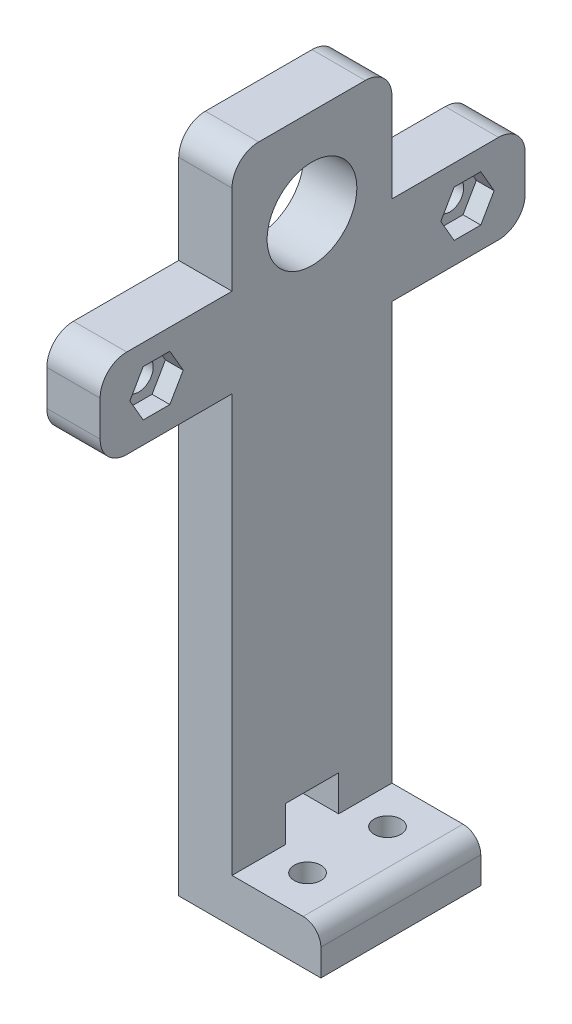
SolidWorks part; units mm, degrees
ref_plane "Front Plane" through (0, 0, 0) normal (0, 0, 1) x (1, 0, 0)
ref_plane "Top Plane" through (0, 0, 0) normal (0, 1, 0) x (1, 0, 0)
ref_plane "Right Plane" through (0, 0, 0) normal (1, 0, 0) x (0, 0, -1)
sketch "Sketch1" plane through (0, 0, 0) normal (0, 1, 0) x (1, 0, 0)
  circle A0 centre (0, 0) radius 17.45
  circle A1 centre (0, 0) radius 12.45
  dimension "D1" = 5
  dimension "D2" = 34.9
extrude "Boss-Extrude1" add sketch "Sketch1" along normal blind 8
sketch "Sketch2" plane through (0, 8, 0) normal (0, 1, 0) x (1, 0, 0)
  circle A0 centre (0, 0) radius 12.45
  circle A1 centre (0, 0) radius 20
  dimension "D1" = 40
extrude "Boss-Extrude2" add sketch "Sketch2" along normal blind 2
sketch "Sketch3" plane through (0, 10, 0) normal (0, 1, 0) x (1, 0, 0)
  circle A0 centre (0, 0) radius 12.45
  circle A1 centre (0, 0) radius 32.5
  dimension "D1" = 65
extrude "Boss-Extrude3" add sketch "Sketch3" along normal blind 4
fillet "Fillet1" radius 1 1 edges at (0, 14, 32.5)
sketch "Sketch10" plane through (0, 14, 0) normal (0, 1, 0) x (1, 0, 0)
  line L1 (30.1869, 9) -> (40.1869, 9)
  line L2 (30.1869, 9) -> (30.1869, -9)
  line L3 (30.1869, -9) -> (40.1869, -9)
  line L4 (40.1869, 9) -> (40.1869, -9)
  line L5 (-30.1869, 9) -> (-40.1869, 9)
  line L6 (-30.1869, 9) -> (-30.1869, -9)
  line L7 (-30.1869, -9) -> (-40.1869, -9)
  line L8 (-40.1869, 9) -> (-40.1869, -9)
  circle A0 centre (0, 0) radius 31.5 construction
  dimension "D1" = 10
  dimension "D2" = 18
extrude "Boss-Extrude6" add sketch "Sketch10" along normal offset from surface (4 mm away) 4 from surface at -4 up to face at (0, 10, 20) starting at face at (0, 10, 20)
sketch "Sketch4" plane through (0, 14, 0) normal (0, 1, 0) x (1, 0, 0)
  line L0 (34.1869, 0) -> (-34.1869, 0) construction
  line L2 (-34.1869, 9) -> (-34.1869, -9)
  line L8 (34.1869, 9) -> (34.1869, -9)
  line L10 (34.1869, 9) -> (40.1869, 9)
  line L11 (40.1869, 9) -> (40.1869, -9)
  line L12 (40.1869, -9) -> (34.1869, -9)
  line L13 (-34.1869, 9) -> (-40.1869, 9)
  line L14 (-40.1869, 9) -> (-40.1869, -9)
  line L15 (-40.1869, -9) -> (-34.1869, -9)
  point P8 (0, 0)
  dimension "D1" = 6
extrude "Boss-Extrude4" add sketch "Sketch4" along normal blind 75 and the other way blind 4
sketch "Sketch5" plane through (34.1869, 0, 0) normal (-1, 0, 0) x (0, 0, 1)
  line L0 (-9, 14) -> (9, 14) construction
  line L1 (-9, 89) -> (9, 89) construction
  circle A0 centre (0, 79) radius 5.05
  point P7 (0, 89)
  dimension "D1" = 10.1
  dimension "D2" = 65
extrude "Cut-Extrude1" cut sketch "Sketch5" against normal blind 113 and the other way blind 306
sketch "Sketch6" plane through (0, 0, -9) normal (0, 0, -1) x (-1, 0, 0)
  line L1 (34.1869, 75.95) -> (40.1869, 75.95)
  line L2 (34.1869, 75.95) -> (34.1869, 65.95)
  line L3 (34.1869, 65.95) -> (40.1869, 65.95)
  line L4 (40.1869, 75.95) -> (40.1869, 65.95)
  line L6 (40.1869, 89) -> (40.1869, 10) construction
  line L7 (34.1869, 14) -> (34.1869, 89) construction
  dimension "D1" = 10
  dimension "D2" = 8
extrude "Boss-Extrude5" add sketch "Sketch6" along normal blind 15 and the other way blind 32.85
sketch "Sketch7" plane through (-34.1869, 0, 0) normal (1, 0, 0) x (0, 0, -1)
  line L0 (-17.5, 71) -> (17.5, 71) construction
  circle A0 centre (-17.5, 71) radius 1.6292
  circle A1 centre (17.5, 71) radius 1.5803
  circle A3 centre (0, 79) radius 4.05 construction
  point P6 (0, 71)
  dimension "D2" = 8
  dimension "D1" = 35
  dimension "D3" = 17.5
extrude "Cut-Extrude2" cut sketch "Sketch7" against normal blind 10
sketch "Sketch9" plane through (-34.1869, 0, 0) normal (1, 0, 0) x (0, 0, -1)
  circle A0 centre (0, 79) radius 5.05
  dimension "D1" = 10.1
extrude "Cut-Extrude3" cut sketch "Sketch9" against normal blind 10 and the other way blind 10
sketch "Sketch11" plane through (34.1869, 0, 0) normal (-1, 0, 0) x (0, 0, 1)
  line L0 (-9, 14) -> (9, 14) construction
  line L1 (4.8913, 14) -> (-4.8913, 14)
  line L2 (4.8913, 14) -> (4.8913, 17.2345)
  line L3 (4.8913, 17.2345) -> (-4.8913, 17.2345)
  line L4 (-4.8913, 14) -> (-4.8913, 17.2345)
  line L5 (9, 10) -> (-9, 10) construction
  point P6 (0, 14)
  point P9 (0, 10)
extrude "Cut-Extrude4" cut sketch "Sketch11" against normal blind 61 and the other way blind 123
fillet "Fillet4" radius 3 6 edges at (-37.1869, 65.95, 23.85) (-37.1869, 75.95, 23.85) (-37.1869, 65.95, -24) (-37.1869, 75.95, -24) (-37.1869, 89, -9) (-37.1869, 89, 9)
fillet "Fillet5" radius 3 2 edges at (40.1869, 10, 0) (-40.1869, 10, 0)
sketch "Sketch12" plane through (40.1869, 0, 0) normal (1, 0, 0) x (0, 0, -1)
  line L0 (9, 10) -> (-9, 10) construction
  line L1 (41.8928, 10) -> (-66.8986, 10)
  line L2 (41.8928, 10) -> (41.8928, -14.0418)
  line L3 (41.8928, -14.0418) -> (-66.8986, -14.0418)
  line L4 (-66.8986, 10) -> (-66.8986, -14.0418)
extrude "Cut-Extrude5" cut sketch "Sketch12" against normal blind 110.678
sketch "Sketch15" plane through (0, 14, 0) normal (0, 1, 0) x (1, 0, 0)
  circle A0 centre (0, 0) radius 22
  dimension "D1" = 44
extrude "Cut-Extrude7" cut sketch "Sketch15" against normal blind 4
sketch "Sketch13" plane through (0, 14, 0) normal (0, 1, 0) x (1, 0, 0)
  line L0 (-15.1554, -8.75) -> (0, 17.5) construction
  line L1 (0, 17.5) -> (15.1554, -8.75) construction
  line L2 (15.1554, -8.75) -> (-15.1554, -8.75) construction
  circle A0 centre (0, 0) radius 11
  circle A1 centre (0, 0) radius 22
  circle A2 centre (0, 0) radius 17.5 construction
  circle A3 centre (0, 17.5) radius 2.75
  circle A4 centre (-15.1554, -8.75) radius 2.75
  circle A5 centre (15.1554, -8.75) radius 2.75
  dimension "D1" = 22
  dimension "D2" = 5.5
  dimension "D3" = 44
  dimension "D5" = 35
  dimension "D4" = 60
extrude "Boss-Extrude7" add sketch "Sketch13" against normal blind 4
fillet "Fillet6" radius 3 2 edges at (37.1869, 89, -9) (37.1869, 89, 9)
sketch "Sketch16" plane through (0, 10, 0) normal (0, -1, 0) x (1, 0, 0)
  line L0 (-31.229, 9) -> (-20.2938, 9)
  line L1 (31.229, 9) -> (20.2938, 9)
  arc A0 (-31.229, 9) -> (31.229, 9) centre (0, 0) cw
  arc A1 (-20.2938, 9) -> (20.2938, 9) centre (0, 0) cw
  dimension "D1" = 22.2
extrude "Cut-Extrude8" cut sketch "Sketch16" against normal blind 5
mirror "Mirror1" about plane through (0, 0, 0) normal (0, 0, 1) of "Cut-Extrude8"
fillet "Fillet7" radius 1 2 edges at (0, 14, 22.2) (0, 14, -22.2)
sketch "Sketch17" plane through (0, 10, 0) normal (0, -1, 0) x (1, 0, 0)
  line L0 (20.2938, -9) -> (40.1869, -9)
  line L1 (40.1869, -9) -> (40.1869, 9)
  line L2 (40.1869, 9) -> (20.2938, 9)
  arc A0 (20.2938, -9) -> (20.2938, 9) centre (0, 0) ccw
  arc A1 (-20.2938, -9) -> (20.2938, -9) centre (0, 0) ccw construction
extrude "Boss-Extrude8" add sketch "Sketch17" along normal blind 6.4 and the other way blind 3
fillet "Fillet8" radius 3 1 edges at (40.1869, 3.6, 0)
mirror "Mirror2" about plane through (0, 0, 0) normal (1, 0, 0) of "Fillet8", "Boss-Extrude8"
sketch "Sketch21" plane through (40.1869, 0, 0) normal (1, 0, 0) x (0, 0, -1)
  circle A0 centre (0, 79) radius 6.05
  dimension "D1" = 12.1
extrude "Cut-Extrude12" cut sketch "Sketch21" along normal blind 3.8 from surface at -6 starting at face at (34.1869, 79, 5.05)
sketch "Sketch18" plane through (40.1869, 0, 0) normal (1, 0, 0) x (0, 0, -1)
  line L1 (44.3735, 99.3869) -> (-44.3735, 99.3869)
  line L2 (44.3735, 99.3869) -> (44.3735, 79)
  line L3 (44.3735, 79) -> (-44.3735, 79)
  line L4 (-44.3735, 99.3869) -> (-44.3735, 79)
  circle A0 centre (0, 79) radius 5.05 construction
  point P4 (0, 79)
extrude "Cut-Extrude9" cut sketch "Sketch18" against normal blind 10
sketch "Sketch19" plane through (0, 79, 0) normal (0, 1, 0) x (1, 0, 0)
  line L0 (40.1869, -9) -> (40.1869, -5.05) construction
  line L1 (34.1869, -6.05) -> (40.1869, -6.05)
  line L2 (34.1869, -6.05) -> (34.1869, -16.5)
  line L3 (34.1869, -16.5) -> (40.1869, -16.5)
  line L4 (40.1869, -6.05) -> (40.1869, -16.5)
  line L5 (34.1869, 6.05) -> (40.1869, 6.05)
  line L6 (34.1869, 6.05) -> (34.1869, 16.5)
  line L7 (34.1869, 16.5) -> (40.1869, 16.5)
  line L8 (40.1869, 6.05) -> (40.1869, 16.5)
  dimension "D1" = 33
extrude "Boss-Extrude9" add sketch "Sketch19" against normal blind 5
fillet "Fillet9" radius 2 2 edges at (37.1869, 74, -16.5) (37.1869, 74, 16.5)
sketch "Sketch22" plane through (-34.1869, 0, 0) normal (1, 0, 0) x (0, 0, -1)
  line L1 (-15.9989, 68.4) -> (-14.4978, 71)
  line L2 (-14.4978, 71) -> (-15.9989, 73.6)
  line L3 (-15.9989, 73.6) -> (-19.0011, 73.6)
  line L4 (-19.0011, 73.6) -> (-20.5022, 71)
  line L5 (-20.5022, 71) -> (-19.0011, 68.4)
  line L6 (-19.0011, 68.4) -> (-15.9989, 68.4)
  line L7 (20.5022, 71) -> (19.0011, 73.6)
  line L8 (19.0011, 73.6) -> (15.9989, 73.6)
  line L9 (15.9989, 73.6) -> (14.4978, 71)
  line L10 (14.4978, 71) -> (15.9989, 68.4)
  line L11 (15.9989, 68.4) -> (19.0011, 68.4)
  line L12 (19.0011, 68.4) -> (20.5022, 71)
  circle A0 centre (-17.5, 71) radius 2.6 construction
  circle A1 centre (17.5, 71) radius 2.6 construction
  dimension "D1" = 5.2
extrude "Cut-Extrude13" cut sketch "Sketch22" against normal blind 2
sketch "Sketch23" plane through (0, 79, 0) normal (0, 1, 0) x (1, 0, 0)
  line L0 (37.1869, -12.3) -> (37.1869, 12.3) construction
  line L1 (34.1869, -16.5) -> (40.1869, -16.5) construction
  line L2 (34.1869, -6.05) -> (34.1869, -16.5) construction
  circle A0 centre (37.1869, -12.3) radius 1
  circle A1 centre (37.1869, 12.3) radius 1
  point P4 (37.1869, 0)
  dimension "D1" = 2
  dimension "D2" = 4.2
  dimension "D3" = 3
extrude "Cut-Extrude14" cut sketch "Sketch23" against normal blind 11
sketch "Sketch24" plane through (0, 74, 0) normal (0, -1, 0) x (1, 0, 0)
  line L1 (37.1869, 9.9906) -> (39.1869, 11.1453)
  line L2 (39.1869, 11.1453) -> (39.1869, 13.4547)
  line L3 (39.1869, 13.4547) -> (37.1869, 14.6094)
  line L4 (37.1869, 14.6094) -> (35.1869, 13.4547)
  line L5 (35.1869, 13.4547) -> (35.1869, 11.1453)
  line L6 (35.1869, 11.1453) -> (37.1869, 9.9906)
  line L7 (37.1869, -14.6094) -> (39.1869, -13.4547)
  line L8 (39.1869, -13.4547) -> (39.1869, -11.1453)
  line L9 (39.1869, -11.1453) -> (37.1869, -9.9906)
  line L10 (37.1869, -9.9906) -> (35.1869, -11.1453)
  line L11 (35.1869, -11.1453) -> (35.1869, -13.4547)
  line L12 (35.1869, -13.4547) -> (37.1869, -14.6094)
  circle A0 centre (37.1869, 12.3) radius 2 construction
  circle A1 centre (37.1869, -12.3) radius 2 construction
  dimension "D1" = 4
extrude "Cut-Extrude16" cut sketch "Sketch24" against normal blind 1.7
ref_plane "Plane1" through (-34.1869, 14, -9) normal (-1, 0, 0) x (0, 0, 1)
sketch "Sketch26" plane through (0, 0, -9) normal (0, 0, -1) x (-1, 0, 0)
  line L0 (34.1869, 9.8772) -> (34.1869, 18.1228) construction
  line L1 (34.1869, 14) -> (34.1869, 94.4914)
  line L2 (34.1869, 94.4914) -> (-54.2516, 94.4914)
  line L3 (-54.2516, 94.4914) -> (-54.2516, -8.9186)
  line L4 (-54.2516, -8.9186) -> (55.5087, -8.9186)
  line L5 (55.5087, -8.9186) -> (55.5087, 14)
  line L6 (55.5087, 14) -> (34.1869, 14)
  line L7 (19.1948, 14) -> (34.1869, 14) construction
extrude "Cut-Extrude17" cut sketch "Sketch26" against normal blind 70 and the other way blind 30
sketch "Sketch27" plane through (-34.1869, 0, 0) normal (1, 0, 0) x (0, 0, -1)
  line L0 (-9, 14) -> (-9, 65.95) construction
  line L1 (9, 14) -> (-9, 14)
  line L2 (9, 14) -> (9, 19)
  line L3 (9, 19) -> (-9, 19)
  line L4 (-9, 14) -> (-9, 19)
  dimension "D1" = 5
extrude "Boss-Extrude10" add sketch "Sketch27" along normal blind 10 and the other way blind 6
fillet "Fillet10" radius 2 1 edges at (-24.1869, 19, 0)
sketch "Sketch28" plane through (-34.1869, 0, 0) normal (1, 0, 0) x (0, 0, -1)
  line L0 (9, 19) -> (-9, 19) construction
  line L1 (3, 19) -> (-3, 19)
  line L2 (3, 19) -> (3, 23)
  line L3 (3, 23) -> (-3, 23)
  line L4 (-3, 19) -> (-3, 23)
  point P4 (0, 19)
  point P7 (0, 19)
  dimension "D1" = 4
  dimension "D2" = 6
extrude "Cut-Extrude18" cut sketch "Sketch28" against normal blind 10
sketch "Sketch29" plane through (0, 19, 0) normal (0, 1, 0) x (1, 0, 0)
  line L0 (-30.1869, 4.5) -> (-30.1869, -4.5) construction
  line L1 (-26.1869, -9) -> (-26.1869, 9) construction
  line L2 (-40.1869, 6) -> (-40.1869, -6) construction
  circle A0 centre (-30.1869, -4.5) radius 1.5
  circle A1 centre (-30.1869, 4.5) radius 1.5
  point P4 (-30.1869, 0)
  point P7 (-26.1869, 0)
  dimension "D1" = 3
  dimension "D2" = 9
  dimension "D3" = 10
extrude "Cut-Extrude19" cut sketch "Sketch29" against normal blind 100
